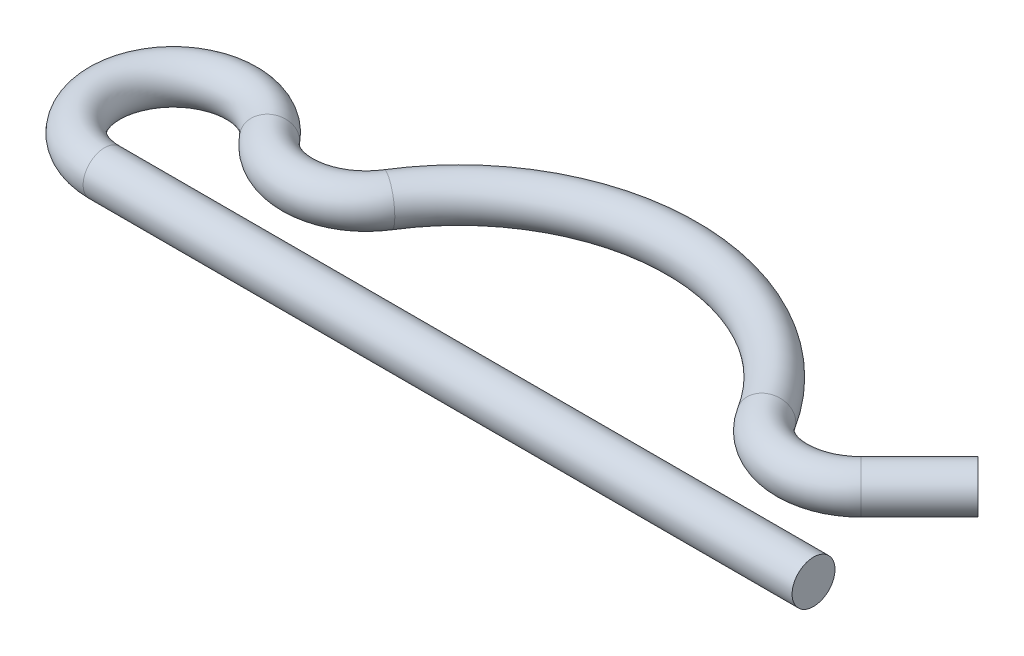
SolidWorks part; units mm, degrees
material "AISI 1020"
ref_plane "Спереди" through (0, 0, 0) normal (0, 0, 1) x (1, 0, 0)
ref_plane "Сверху" through (0, 0, 0) normal (0, 1, 0) x (1, 0, 0)
ref_plane "Справа" through (0, 0, 0) normal (1, 0, 0) x (0, 0, -1)
sketch "Эскиз1" plane through (0, 0, 0) normal (0, 1, 0) x (1, 0, 0)
  line L0 (20.6672, 0) -> (-20.6672, 0)
  line L1 (7.5498, 1.75) -> (-7.5498, 1.75) construction
  line L2 (17.2506, 6.1716) -> (20.6672, 9.5881)
  arc A0 (-11.0287, 6.8824) -> (11.0287, 6.8824) centre (0, 0) cw
  arc A1 (-11.0287, 6.8824) -> (-17.5447, 6.5) centre (-14.4222, 9) cw
  arc A2 (-17.5447, 6.5) -> (-20.6672, 0) centre (-20.6672, 4) ccw
  arc A3 (11.0287, 6.8824) -> (17.2506, 6.1716) centre (14.4222, 9) ccw
  circle A4 centre (0, 0) radius 10 construction
  point P17 (0, 0)
  dimension "D1" = 3
  dimension "D3" = 5
  dimension "D5" = 4
  dimension "D2" = 5
  dimension "D4" = 45
ref_plane "Плоскость1" through (20.6672, 0, 0) normal (-1, 0, 0) x (0, 0, 1)
sketch "Эскиз2" plane through (20.6672, 0, 0) normal (-1, 0, 0) x (0, 0, 1)
  circle A0 centre (0, 0) radius 1.25
  dimension "D1" = 2.5
sweep "По траектории1" add profiles "Эскиз2" path "Эскиз1"
